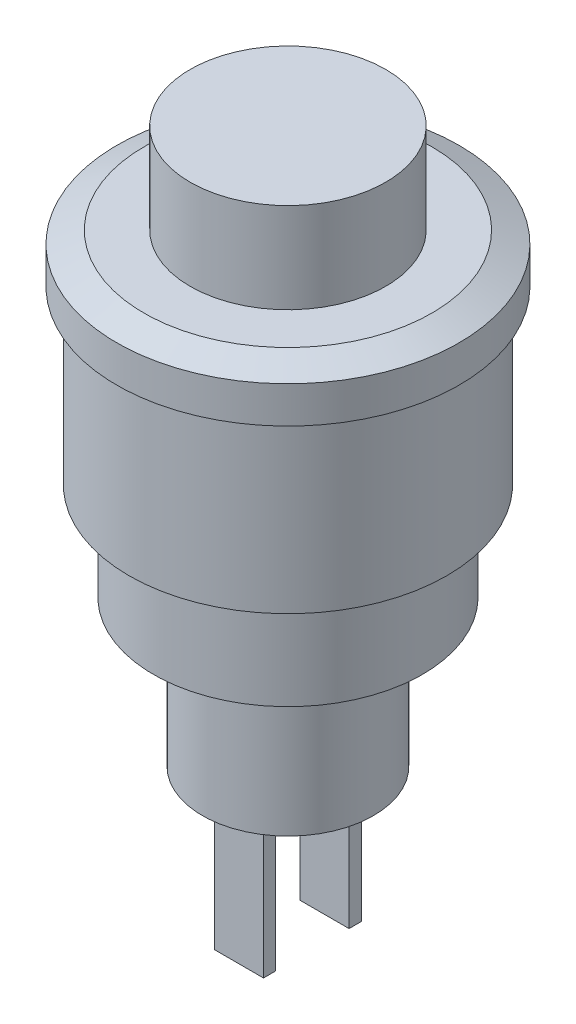
SolidWorks part; units mm, degrees
ref_plane "Plano frontal" through (0, 0, 0) normal (0, 0, 1) x (1, 0, 0)
ref_plane "Plano superior" through (0, 0, 0) normal (0, 1, 0) x (1, 0, 0)
ref_plane "Plano direito" through (0, 0, 0) normal (1, 0, 0) x (0, 0, -1)
sketch "Esboço1" plane through (0, 0, 0) normal (0, 0, 1) x (1, 0, 0)
  line L0 (0, 22.6898) -> (4, 22.6898)
  line L1 (4, 22.6898) -> (4, 19)
  line L2 (4, 19) -> (5.8913, 19)
  line L3 (5.8913, 19) -> (7, 18.5)
  line L4 (7, 18.5) -> (7, 17)
  line L5 (7, 17) -> (6.5, 17)
  line L6 (6.5, 17) -> (6.5, 10)
  line L7 (6.5, 10) -> (5.5, 10)
  line L8 (5.5, 10) -> (5.5, 6)
  line L9 (5.5, 6) -> (3.5, 6)
  line L10 (3.5, 6) -> (3.5, 0)
  line L11 (3.5, 0) -> (0, 0)
  line L12 (0, 0) -> (0, 22.6898)
  dimension "D1" = 4
  dimension "D2" = 6
  dimension "D3" = 7
  dimension "D4" = 1
  dimension "D5" = 2
  dimension "D6" = 3.5
  dimension "D7" = 4
  dimension "D8" = 7
  dimension "D9" = 2
  dimension "D10" = 1.5
revolve "Revolução1" add sketch "Esboço1" angle 360 about L12
sketch "Esboço2" plane through (0, 0, 0) normal (0, -1, 0) x (1, 0, 0)
  line L0 (1.4586, 0) -> (-1.2654, 0) construction
  line L1 (1, -1.5) -> (-1, -1.5)
  line L2 (1, -1.5) -> (1, -2)
  line L3 (1, -2) -> (-1, -2)
  line L4 (-1, -1.5) -> (-1, -2)
  line L5 (1, 2) -> (-1, 2)
  line L6 (-1, 1.5) -> (-1, 2)
  line L7 (1, 1.5) -> (-1, 1.5)
  line L8 (1, 1.5) -> (1, 2)
  point P4 (-1, -1.75)
  point P12 (0, -1.5)
  dimension "D1" = 0.5
  dimension "D2" = 2
  dimension "D3" = 2
extrude "Ressalto-extrusão1" add sketch "Esboço2" along normal blind 6
